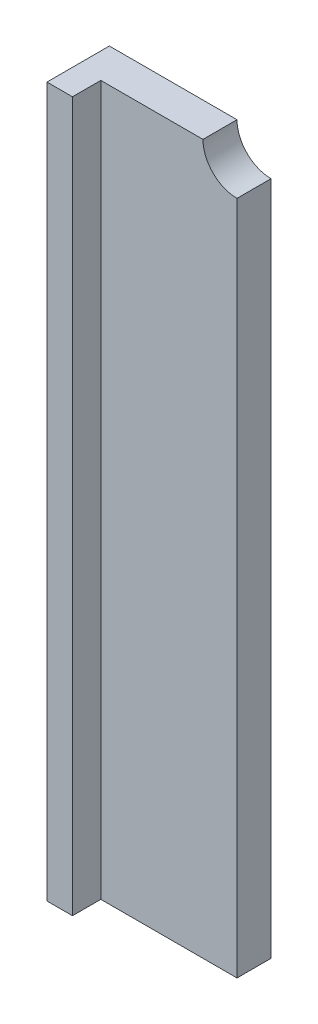
SolidWorks part; units mm, degrees
ref_plane "Alzado" through (0, 0, 0) normal (0, 0, 1) x (1, 0, 0)
ref_plane "Planta" through (0, 0, 0) normal (0, 1, 0) x (1, 0, 0)
ref_plane "Vista lateral" through (0, 0, 0) normal (1, 0, 0) x (0, 0, -1)
sketch "Croquis1" plane through (0, 0, 0) normal (0, 0, 1) x (1, 0, 0)
  line L1 (0, 0) -> (28.5, 0)
  line L2 (0, 0) -> (0, 125)
  line L3 (0, 125) -> (28.5, 125)
  line L4 (28.5, 0) -> (28.5, 125)
  dimension "D1" = 125
  dimension "D2" = 28.5
extrude "Saliente-Extruir1" add sketch "Croquis1" along normal blind 6
sketch "Croquis2" plane through (0, 0, 6) normal (0, 0, 1) x (1, 0, 0)
  line L0 (28.5, 125) -> (0, 125) construction
  line L1 (0, 0) -> (4.5, 0)
  line L2 (0, 0) -> (0, 125)
  line L3 (0, 125) -> (4.5, 125)
  line L4 (4.5, 0) -> (4.5, 125)
  dimension "D1" = 4.5
extrude "Saliente-Extruir2" add sketch "Croquis2" along normal blind 5
sketch "Croquis3" plane through (0, 0, 6) normal (0, 0, 1) x (1, 0, 0)
  circle A0 centre (28.5, 125) radius 6
  dimension "D1" = 12
extrude "Cortar-Extruir1" cut sketch "Croquis3" against normal through all
